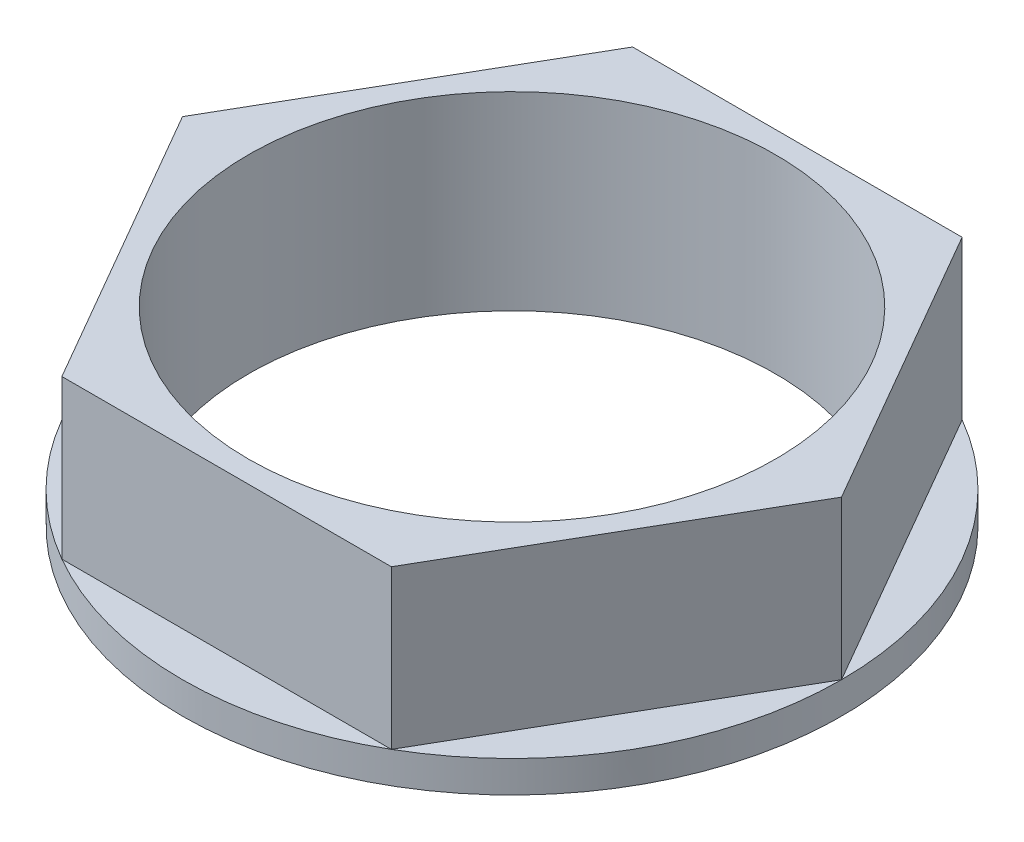
SolidWorks part; units mm, degrees
ref_plane "Front Plane" through (0, 0, 0) normal (0, 0, 1) x (1, 0, 0)
ref_plane "Top Plane" through (0, 0, 0) normal (0, 1, 0) x (1, 0, 0)
ref_plane "Right Plane" through (0, 0, 0) normal (1, 0, 0) x (0, 0, -1)
sketch "Sketch1" plane through (0, 0, 0) normal (0, 1, 0) x (1, 0, 0)
  circle A0 centre (0, 0) radius 7.9375
  dimension "D1" = 15.875
extrude "Boss-Extrude1" add sketch "Sketch1" along normal mid plane 0.762
sketch "Sketch2" plane through (0, 0.381, 0) normal (0, 1, 0) x (1, 0, 0)
  line L1 (-3.9688, -6.8741) -> (3.9687, -6.8741)
  line L2 (3.9687, -6.8741) -> (7.9375, 0)
  line L3 (7.9375, 0) -> (3.9687, 6.8741)
  line L4 (3.9687, 6.8741) -> (-3.9687, 6.8741)
  line L5 (-3.9687, 6.8741) -> (-7.9375, 0)
  line L6 (-7.9375, 0) -> (-3.9688, -6.8741)
  circle A0 centre (0, 0) radius 6.8741 construction
  dimension "D1" = 13.7482
extrude "Boss-Extrude2" add sketch "Sketch2" along normal blind 3.81
sketch "Sketch3" plane through (0, 4.191, 0) normal (0, 1, 0) x (1, 0, 0)
  circle A0 centre (0, 0) radius 6.35
  dimension "D1" = 12.7
extrude "Cut-Extrude1" cut sketch "Sketch3" against normal through all
